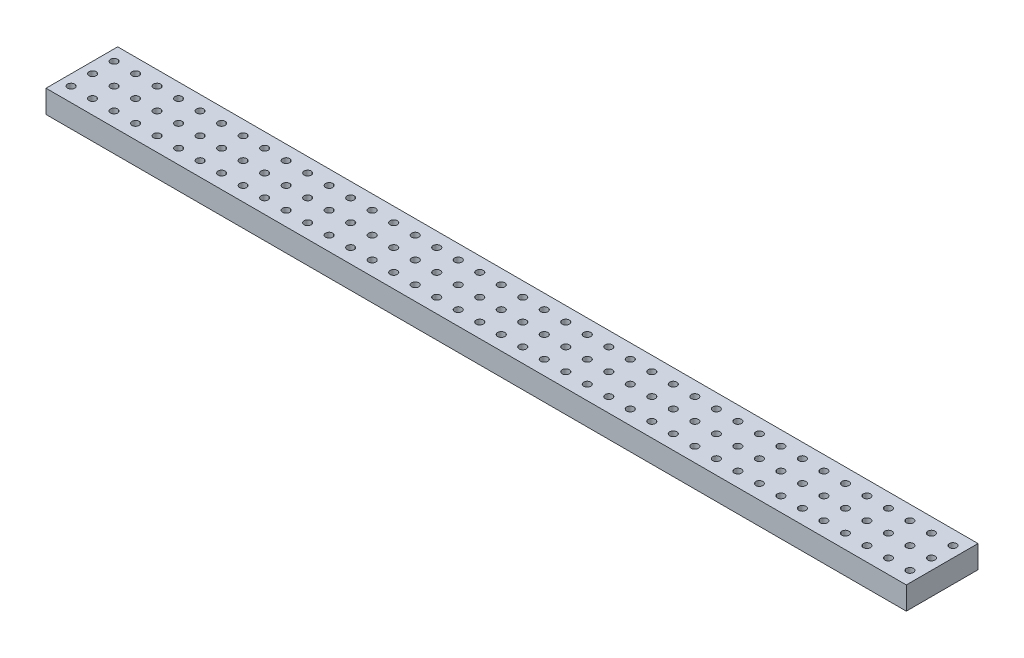
SolidWorks part; units mm, degrees
ref_plane "Front Plane" through (0, 0, 0) normal (0, 0, 1) x (1, 0, 0)
ref_plane "Top Plane" through (0, 0, 0) normal (0, 1, 0) x (1, 0, 0)
ref_plane "Right Plane" through (0, 0, 0) normal (1, 0, 0) x (0, 0, -1)
sketch "Sketch1" plane through (0, 0, 0) normal (0, 1, 0) x (1, 0, 0)
  line L5 (0, 10) -> (120, 10)
  line L6 (0, 10) -> (0, 0)
  line L7 (0, 0) -> (120, 0)
  line L8 (120, 10) -> (120, 0)
  circle A0 centre (1.5, 8) radius 0.5
  circle A1 centre (1.5, 5) radius 0.5
  circle A2 centre (1.5, 2) radius 0.5
  circle A3 centre (4.5, 8) radius 0.5
  circle A4 centre (4.5, 5) radius 0.5
  circle A5 centre (4.5, 2) radius 0.5
  circle A6 centre (7.5, 8) radius 0.5
  circle A7 centre (7.5, 5) radius 0.5
  circle A8 centre (7.5, 2) radius 0.5
  circle A9 centre (10.5, 8) radius 0.5
  circle A10 centre (10.5, 5) radius 0.5
  circle A11 centre (10.5, 2) radius 0.5
  circle A12 centre (13.5, 8) radius 0.5
  circle A13 centre (13.5, 5) radius 0.5
  circle A14 centre (13.5, 2) radius 0.5
  circle A15 centre (16.5, 8) radius 0.5
  circle A16 centre (16.5, 5) radius 0.5
  circle A17 centre (16.5, 2) radius 0.5
  circle A18 centre (19.5, 8) radius 0.5
  circle A19 centre (19.5, 5) radius 0.5
  circle A20 centre (19.5, 2) radius 0.5
  circle A21 centre (22.5, 8) radius 0.5
  circle A22 centre (22.5, 5) radius 0.5
  circle A23 centre (22.5, 2) radius 0.5
  circle A24 centre (25.5, 8) radius 0.5
  circle A25 centre (25.5, 5) radius 0.5
  circle A26 centre (25.5, 2) radius 0.5
  circle A27 centre (28.5, 8) radius 0.5
  circle A28 centre (28.5, 5) radius 0.5
  circle A29 centre (28.5, 2) radius 0.5
  circle A30 centre (31.5, 8) radius 0.5
  circle A31 centre (31.5, 5) radius 0.5
  circle A32 centre (31.5, 2) radius 0.5
  circle A33 centre (34.5, 8) radius 0.5
  circle A34 centre (34.5, 5) radius 0.5
  circle A35 centre (34.5, 2) radius 0.5
  circle A36 centre (37.5, 8) radius 0.5
  circle A37 centre (37.5, 5) radius 0.5
  circle A38 centre (37.5, 2) radius 0.5
  circle A39 centre (40.5, 8) radius 0.5
  circle A40 centre (40.5, 5) radius 0.5
  circle A41 centre (40.5, 2) radius 0.5
  circle A42 centre (43.5, 8) radius 0.5
  circle A43 centre (43.5, 5) radius 0.5
  circle A44 centre (43.5, 2) radius 0.5
  circle A45 centre (46.5, 8) radius 0.5
  circle A46 centre (46.5, 5) radius 0.5
  circle A47 centre (46.5, 2) radius 0.5
  circle A48 centre (49.5, 8) radius 0.5
  circle A49 centre (49.5, 5) radius 0.5
  circle A50 centre (49.5, 2) radius 0.5
  circle A51 centre (52.5, 8) radius 0.5
  circle A52 centre (52.5, 5) radius 0.5
  circle A53 centre (52.5, 2) radius 0.5
  circle A54 centre (55.5, 8) radius 0.5
  circle A55 centre (55.5, 5) radius 0.5
  circle A56 centre (55.5, 2) radius 0.5
  circle A57 centre (58.5, 8) radius 0.5
  circle A58 centre (58.5, 5) radius 0.5
  circle A59 centre (58.5, 2) radius 0.5
  circle A60 centre (61.5, 8) radius 0.5
  circle A61 centre (61.5, 5) radius 0.5
  circle A62 centre (61.5, 2) radius 0.5
  circle A63 centre (64.5, 8) radius 0.5
  circle A64 centre (64.5, 5) radius 0.5
  circle A65 centre (64.5, 2) radius 0.5
  circle A66 centre (67.5, 8) radius 0.5
  circle A67 centre (67.5, 5) radius 0.5
  circle A68 centre (67.5, 2) radius 0.5
  circle A69 centre (70.5, 8) radius 0.5
  circle A70 centre (70.5, 5) radius 0.5
  circle A71 centre (70.5, 2) radius 0.5
  circle A72 centre (73.5, 8) radius 0.5
  circle A73 centre (73.5, 5) radius 0.5
  circle A74 centre (73.5, 2) radius 0.5
  circle A75 centre (76.5, 8) radius 0.5
  circle A76 centre (76.5, 5) radius 0.5
  circle A77 centre (76.5, 2) radius 0.5
  circle A78 centre (79.5, 8) radius 0.5
  circle A79 centre (79.5, 5) radius 0.5
  circle A80 centre (79.5, 2) radius 0.5
  circle A81 centre (82.5, 8) radius 0.5
  circle A82 centre (82.5, 5) radius 0.5
  circle A83 centre (82.5, 2) radius 0.5
  circle A84 centre (85.5, 8) radius 0.5
  circle A85 centre (85.5, 5) radius 0.5
  circle A86 centre (85.5, 2) radius 0.5
  circle A87 centre (88.5, 8) radius 0.5
  circle A88 centre (88.5, 5) radius 0.5
  circle A89 centre (88.5, 2) radius 0.5
  circle A90 centre (91.5, 8) radius 0.5
  circle A91 centre (91.5, 5) radius 0.5
  circle A92 centre (91.5, 2) radius 0.5
  circle A93 centre (94.5, 8) radius 0.5
  circle A94 centre (94.5, 5) radius 0.5
  circle A95 centre (94.5, 2) radius 0.5
  circle A96 centre (97.5, 8) radius 0.5
  circle A97 centre (97.5, 5) radius 0.5
  circle A98 centre (97.5, 2) radius 0.5
  circle A99 centre (100.5, 8) radius 0.5
  circle A100 centre (100.5, 5) radius 0.5
  circle A101 centre (100.5, 2) radius 0.5
  circle A102 centre (103.5, 8) radius 0.5
  circle A103 centre (103.5, 5) radius 0.5
  circle A104 centre (103.5, 2) radius 0.5
  circle A105 centre (106.5, 8) radius 0.5
  circle A106 centre (106.5, 5) radius 0.5
  circle A107 centre (106.5, 2) radius 0.5
  circle A108 centre (109.5, 8) radius 0.5
  circle A109 centre (109.5, 5) radius 0.5
  circle A110 centre (109.5, 2) radius 0.5
  circle A111 centre (112.5, 8) radius 0.5
  circle A112 centre (112.5, 5) radius 0.5
  circle A113 centre (112.5, 2) radius 0.5
  circle A114 centre (115.5, 8) radius 0.5
  circle A115 centre (115.5, 5) radius 0.5
  circle A116 centre (115.5, 2) radius 0.5
  circle A117 centre (118.5, 8) radius 0.5
  circle A118 centre (118.5, 5) radius 0.5
  circle A119 centre (118.5, 2) radius 0.5
  point P11 (0, 5)
  dimension "D3" = 1
  dimension "D1" = 120
  dimension "D2" = 10
  dimension "D4" = 3
  dimension "D5" = 3
  dimension "D6" = 1.5
  dimension "D7" = 40
extrude "Boss-Extrude1" add sketch "Sketch1" along normal blind 3.175
